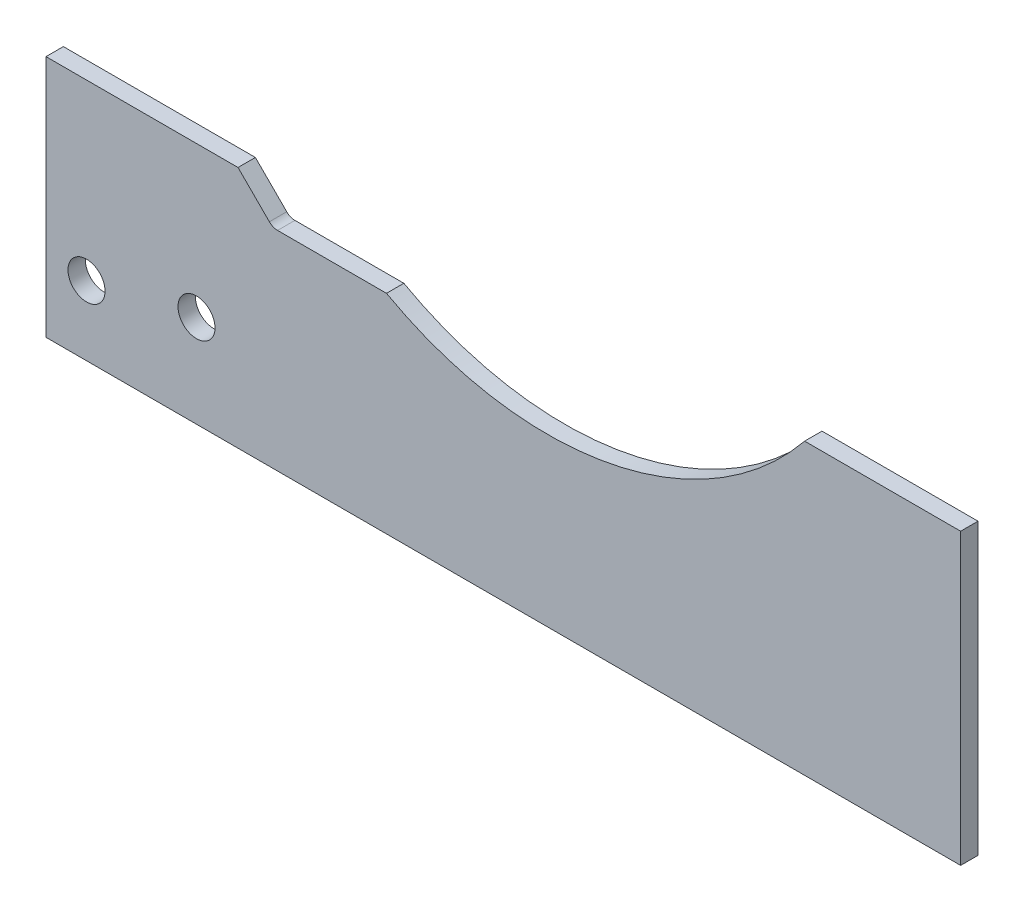
SolidWorks part; units mm, degrees
material "PA Тип 6"
ref_plane "Спереди" through (0, 0, 0) normal (0, 0, 1) x (1, 0, 0)
ref_plane "Сверху" through (0, 0, 0) normal (0, 1, 0) x (1, 0, 0)
ref_plane "Справа" through (0, 0, 0) normal (1, 0, 0) x (0, 0, -1)
sketch "Эскиз1" plane through (0, 0, 0) normal (0, 0, 1) x (1, 0, 0)
  line L0 (0, 21) -> (0, 0)
  line L1 (16.586, 21) -> (19.2931, 18.2929)
  line L2 (79, 0) -> (79, 25)
  line L3 (0, 21) -> (16.586, 21)
  line L4 (20.0002, 18) -> (29.409, 18)
  line L5 (79, 25) -> (65.5252, 25)
  line L6 (0, 0) -> (79, 0)
  circle A0 centre (3.5, 6) radius 1.6
  circle A1 centre (13, 8) radius 1.6
  arc A2 (19.2931, 18.2929) -> (20.0002, 18) centre (20.0002, 19) ccw
  arc A17 (29.409, 18) -> (65.5252, 25) centre (43.3, 43) ccw
  dimension "D6" = 28.6
  dimension "D8" = 43
  dimension "D9" = 1
  dimension "D11" = 3.5
  dimension "D12" = 3.2
  dimension "D14" = 8
  dimension "D1" = 79
  dimension "D2" = 25
  dimension "D3" = 21
  dimension "D4" = 45
  dimension "D5" = 3
  dimension "D7" = 43.3
  dimension "D10" = 6
  dimension "D13" = 13
  dimension "D15" = 16.586
extrude "Бобышка-Вытянуть1" add sketch "Эскиз1" along normal blind 1.5
